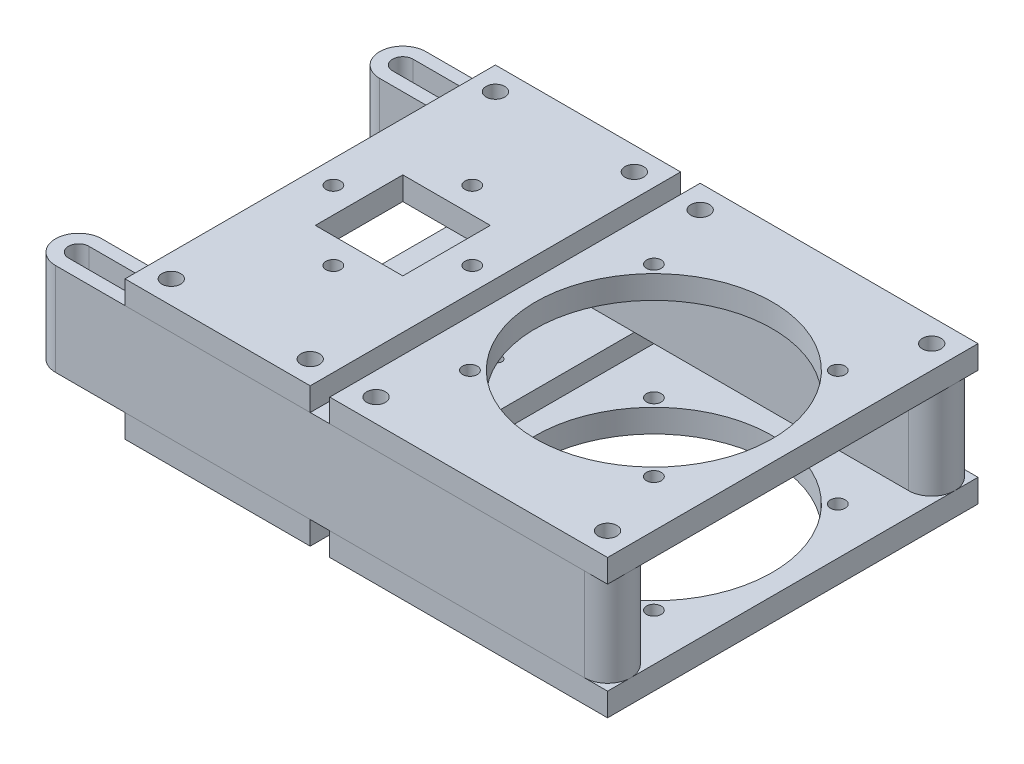
SolidWorks part; units mm, degrees
other "Modual Holding Plate 2"
other "Modual Holding Plate"
other "Encoder Mount Plate"
other "Gearbox Mount Plate"
other "Tension Slider"
other "Tension Slider 2"
material "Alum Plate"
ref_plane "Front Plane" through (0, 0, 0) normal (0, 0, 1) x (1, 0, 0)
ref_plane "Top Plane" through (0, 0, 0) normal (0, 1, 0) x (1, 0, 0)
ref_plane "Right Plane" through (0, 0, 0) normal (1, 0, 0) x (0, 0, -1)
sketch "Sketch2" plane through (0, 0, 0) normal (0, 1, 0) x (1, 0, 0)
  line L0 (0, 0) -> (-68.8619, 0) construction
  line L1 (-38.1, -50.8) -> (-38.1, 50.8)
  line L2 (-38.1, 50.8) -> (38.1, 50.8)
  line L4 (-38.1, -50.8) -> (38.1, -50.8)
  line L5 (38.1, 50.8) -> (38.1, -50.8)
  line L7 (-94.2619, 50.8) -> (-43.4619, 50.8)
  line L8 (-80.8619, 12) -> (-56.8619, 12) construction
  line L9 (-80.8619, 12) -> (-80.8619, -12) construction
  line L10 (-80.8619, -12) -> (-56.8619, -12) construction
  line L11 (-56.8619, 12) -> (-56.8619, -12) construction
  line L12 (-80.8619, 12) -> (-56.8619, -12) construction
  line L13 (-80.8619, -12) -> (-56.8619, 12) construction
  line L14 (-38.1, -50.8) -> (38.1, 50.8) construction
  line L15 (-94.2619, 50.8) -> (-94.2619, -50.8)
  line L16 (-94.2619, -50.8) -> (-43.4619, -50.8)
  line L17 (-43.4619, 50.8) -> (-43.4619, -50.8)
  line L18 (-94.2619, 50.8) -> (-43.4619, -50.8) construction
  line L19 (-94.2619, -50.8) -> (-43.4619, 50.8) construction
  circle A0 centre (0, 0) radius 32.5
  circle A1 centre (-68.8619, 0) radius 18 construction
  point P5 (-34.431, 0)
  point P8 (-38.1, 0)
  dimension "D1" = 65
  dimension "D2" = 36
  dimension "D3" = 68.8619
  dimension "D4" = 38.1
  dimension "D5" = 50.8
  dimension "D6" = 24
  dimension "D8" = 50.8
extrude "Boss-Extrude1" add sketch "Sketch2" against normal blind 6.35 from offset 19.05
mirror "Mirror1" about plane through (0, 0, 0) normal (0, 1, 0) of bodies 101 109
sketch "Sketch3" plane through (0, 19.05, 0) normal (0, 1, 0) x (1, 0, 0)
  line L1 (-80.8619, -12) -> (-56.8619, -12)
  line L2 (-80.8619, -12) -> (-80.8619, 12)
  line L3 (-80.8619, 12) -> (-56.8619, 12)
  line L4 (-56.8619, -12) -> (-56.8619, 12)
  line L5 (-80.8619, -12) -> (-56.8619, 12) construction
  line L6 (-80.8619, 12) -> (-56.8619, -12) construction
  point P4 (-68.8619, 0)
extrude "Cut-Extrude1" cut sketch "Sketch3" against normal up to next (6.35 mm away)
sketch "Sketch4" plane through (0, -19.05, 0) normal (0, -1, 0) x (1, 0, 0)
  circle A1 centre (-68.8619, 0) radius 11.176
  dimension "D1" = 22.352
extrude "Cut-Extrude2" cut sketch "Sketch4" against normal up to next (6.35 mm away)
sketch "Sketch5" plane through (0, -19.05, 0) normal (0, -1, 0) x (1, 0, 0)
  line L1 (-81.8667, 13.0048) -> (-55.8571, 13.0048) construction
  line L2 (-81.8667, 13.0048) -> (-81.8667, -13.0048) construction
  line L3 (-81.8667, -13.0048) -> (-55.8571, -13.0048) construction
  line L4 (-55.8571, 13.0048) -> (-55.8571, -13.0048) construction
  line L5 (-81.8667, 13.0048) -> (-55.8571, -13.0048) construction
  line L6 (-81.8667, -13.0048) -> (-55.8571, 13.0048) construction
  circle A0 centre (-81.8667, 13.0048) radius 1.25
  circle A1 centre (-55.8571, 13.0048) radius 1.25
  circle A2 centre (-55.8571, -13.0048) radius 1.25
  circle A3 centre (-81.8667, -13.0048) radius 1.25
  point P0 (-68.8619, 0)
  dimension "D2" = 2.5
  dimension "D1" = 26.0096
extrude "Cut-Extrude3" cut sketch "Sketch5" against normal up to next (6.35 mm away)
sketch "Sketch6" plane through (0, 19.05, 0) normal (0, 1, 0) x (1, 0, 0)
  line L0 (-38.1, -44.45) -> (-31.75, -44.45) construction
  line L2 (-31.75, -44.45) -> (-31.75, -50.8) construction
  line L3 (-38.1, -50.8) -> (38.1, -50.8) construction
  line L4 (-38.1, 44.45) -> (-31.75, 44.45) construction
  line L5 (-31.75, 44.45) -> (-31.75, 50.8) construction
  line L6 (38.1, 50.8) -> (-38.1, 50.8) construction
  line L7 (38.1, 44.45) -> (31.75, 44.45) construction
  line L8 (38.1, -50.8) -> (38.1, 50.8) construction
  line L9 (31.75, 44.45) -> (31.75, 50.8) construction
  line L10 (31.75, -50.8) -> (31.75, -44.45) construction
  line L11 (31.75, -44.45) -> (38.1, -44.45) construction
  line L12 (-38.1, 50.8) -> (-38.1, -50.8) construction
  line L13 (25.226, 25.226) -> (-25.226, 25.226) construction
  line L14 (25.226, 25.226) -> (25.226, -25.226) construction
  line L15 (25.226, -25.226) -> (-25.226, -25.226) construction
  line L16 (-25.226, 25.226) -> (-25.226, -25.226) construction
  line L17 (25.226, 25.226) -> (-25.226, -25.226) construction
  line L18 (25.226, -25.226) -> (-25.226, 25.226) construction
  line L19 (-49.8119, -50.8) -> (-49.8119, -44.45) construction
  line L20 (-94.2619, -50.8) -> (-43.4619, -50.8) construction
  line L21 (-49.8119, -44.45) -> (-43.4619, -44.45) construction
  line L22 (-43.4619, -50.8) -> (-43.4619, 50.8) construction
  line L23 (-68.8619, -50.8) -> (-68.8619, 50.8) construction
  line L24 (-43.4619, 50.8) -> (-94.2619, 50.8) construction
  line L25 (-94.2619, 0) -> (-43.4619, 0) construction
  line L26 (-94.2619, 50.8) -> (-94.2619, -50.8) construction
  circle A0 centre (-31.75, 44.45) radius 2.5527
  circle A1 centre (31.75, 44.45) radius 2.5527
  circle A2 centre (31.75, -44.45) radius 2.5527
  circle A3 centre (-31.75, -44.45) radius 2.5527
  circle A4 centre (-25.226, 25.226) radius 2.0193
  circle A5 centre (25.226, 25.226) radius 2.0193
  circle A6 centre (25.226, -25.226) radius 2.0193
  circle A7 centre (-25.226, -25.226) radius 2.0193
  circle A8 centre (0, 0) radius 32.5 construction
  circle A9 centre (-49.8119, -44.45) radius 2.5527
  circle A10 centre (-49.8119, 44.45) radius 2.5527
  circle A11 centre (-87.9119, -44.45) radius 2.5527
  circle A12 centre (-87.9119, 44.45) radius 2.5527
  point P24 (0, 0)
  point P34 (-22.981, 22.981)
  dimension "D2" = 5.1054
  dimension "D3" = 4.0386
  dimension "D1" = 6.35
  dimension "D4" = 3.175
extrude "Cut-Extrude4" cut sketch "Sketch6" against normal through all
sketch "Sketch7" plane through (0, 19.05, 0) normal (0, 1, 0) x (1, 0, 0)
  line L0 (-68.8619, -19.05) -> (-68.8619, 0) construction
  line L1 (-68.8619, 0) -> (-68.8619, 19.05) construction
  line L2 (-49.8119, 0) -> (-68.8619, 0) construction
  line L3 (-68.8619, 0) -> (-87.9119, 0) construction
  circle A0 centre (-68.8619, 19.05) radius 2.0193
  circle A1 centre (-68.8619, -19.05) radius 2.0193
  circle A2 centre (-87.9119, 0) radius 2.0193
  circle A3 centre (-49.8119, 0) radius 2.0193
  dimension "D1" = 4.0386
  dimension "D2" = 19.05
extrude "Cut-Extrude5" cut sketch "Sketch7" against normal up to next (6.35 mm away)
sketch "Sketch8" plane through (0, -12.7, 0) normal (0, 1, 0) x (1, 0, 0)
  line L0 (31.75, -44.45) -> (-113.3119, -44.45) construction
  line L1 (31.75, -50.8) -> (-113.3119, -50.8)
  line L2 (31.75, -38.1) -> (-113.3119, -38.1)
  line L3 (-94.2619, -50.8) -> (-43.4619, -50.8) construction
  line L4 (31.75, 44.45) -> (-113.3119, 44.45) construction
  line L5 (31.75, 38.1) -> (-113.3119, 38.1)
  line L6 (31.75, 50.8) -> (-113.3119, 50.8)
  line L7 (-43.4619, 50.8) -> (-94.2619, 50.8) construction
  line L8 (-113.3119, -44.45) -> (-113.3119, 44.45) construction
  line L9 (-49.8119, 44.45) -> (-113.3119, 44.45) construction
  line L10 (-49.8119, 41.656) -> (-113.3119, 41.656)
  line L11 (-49.8119, 47.244) -> (-113.3119, 47.244)
  line L12 (-49.8119, -44.45) -> (-113.3119, -44.45) construction
  line L13 (-49.8119, -47.244) -> (-113.3119, -47.244)
  line L14 (-49.8119, -41.656) -> (-113.3119, -41.656)
  arc A0 (31.75, -50.8) -> (31.75, -38.1) centre (31.75, -44.45) ccw
  arc A1 (-113.3119, -38.1) -> (-113.3119, -50.8) centre (-113.3119, -44.45) ccw
  arc A2 (31.75, 38.1) -> (31.75, 50.8) centre (31.75, 44.45) ccw
  arc A3 (-113.3119, 50.8) -> (-113.3119, 38.1) centre (-113.3119, 44.45) ccw
  arc A6 (-49.8119, 41.656) -> (-49.8119, 47.244) centre (-49.8119, 44.45) ccw
  arc A7 (-113.3119, 47.244) -> (-113.3119, 41.656) centre (-113.3119, 44.45) ccw
  arc A8 (-49.8119, -47.244) -> (-49.8119, -41.656) centre (-49.8119, -44.45) ccw
  arc A9 (-113.3119, -41.656) -> (-113.3119, -47.244) centre (-113.3119, -44.45) ccw
  circle A10 centre (31.75, -44.45) radius 2.5527 construction
  circle A11 centre (31.75, 44.45) radius 2.5527 construction
  circle A12 centre (-31.75, 44.45) radius 2.5527 construction
  circle A13 centre (-31.75, -44.45) radius 2.5527 construction
  circle A14 centre (-31.75, -44.45) radius 2.5527
  circle A15 centre (-31.75, 44.45) radius 2.5527
  circle A16 centre (31.75, 44.45) radius 2.5527
  circle A17 centre (31.75, -44.45) radius 2.5527
  point P3 (-40.781, -44.45)
  point P13 (-40.781, 44.45)
  point P23 (-87.9119, 44.45)
  point P24 (-81.5619, 44.45)
  point P32 (-81.5619, -44.45)
  dimension "D1" = 25.4
  dimension "D2" = 5.588
extrude "Boss-Extrude2" add sketch "Sketch8" along normal up to surface (25.4 mm away) separate body up to face at (-87.9119, 12.7, 2.0193)
other "Save Bodies1"
